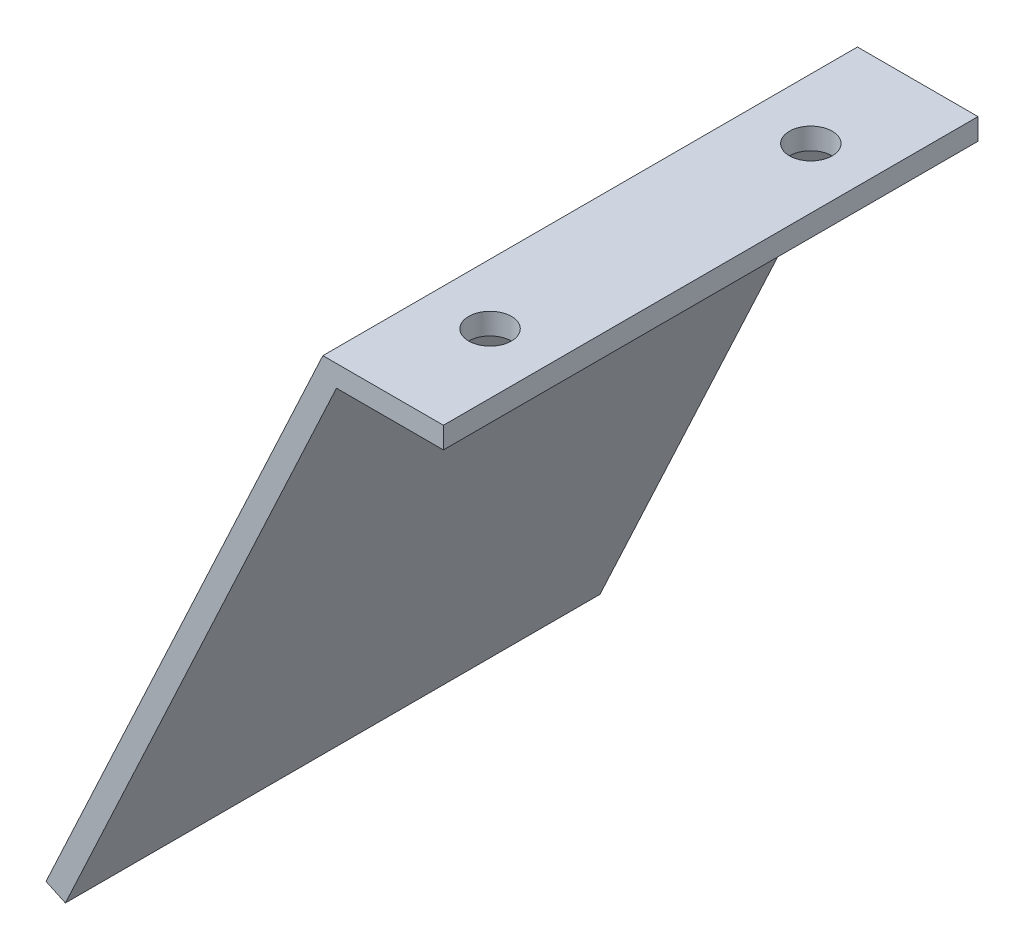
SolidWorks part; units mm, degrees
material "ABS"
ref_plane "Front Plane" through (0, 0, 0) normal (0, 0, 1) x (1, 0, 0)
ref_plane "Top Plane" through (0, 0, 0) normal (0, 1, 0) x (1, 0, 0)
ref_plane "Right Plane" through (0, 0, 0) normal (1, 0, 0) x (0, 0, -1)
sketch "Sketch1" plane through (0, 0, 0) normal (0, 0, 1) x (1, 0, 0)
  line L0 (0, 0) -> (-10, 0)
  line L1 (-10, 0) -> (-35.3571, -54.3785)
  line L2 (-35.3571, -54.3785) -> (-37.1697, -53.5332)
  line L3 (-37.1697, -53.5332) -> (-11.2741, 2)
  line L4 (-11.2741, 2) -> (0, 2)
  line L5 (0, 2) -> (0, 0)
  dimension "D1" = 2
  dimension "D2" = 2
  dimension "D3" = 115
  dimension "D4" = 10
  dimension "D5" = 60
extrude "Boss-Extrude1" add sketch "Sketch1" along normal blind 50
sketch "Sketch2" plane through (0, 2, 0) normal (0, 1, 0) x (1, 0, 0)
  line L0 (-5.6371, 6.0457) -> (-5.6371, -54.1718) construction
  line L1 (-18.2291, -10) -> (5.9044, -10) construction
  line L2 (-18.2291, -40) -> (8.8532, -40) construction
  line L3 (-21.2555, -25) -> (14.0524, -25) construction
  line L4 (0, 0) -> (-11.2741, 0) construction
  line L5 (0, -50) -> (0, 0) construction
  circle A0 centre (-5.6371, -10) radius 2
  circle A1 centre (-5.6371, -40) radius 2
  point P10 (-5.6371, 0)
  point P13 (0, -25)
  dimension "D3" = 4
  dimension "D4" = 4
  dimension "D1" = 15
  dimension "D2" = 15
extrude "Cut-Extrude1" cut sketch "Sketch2" against normal up to next
